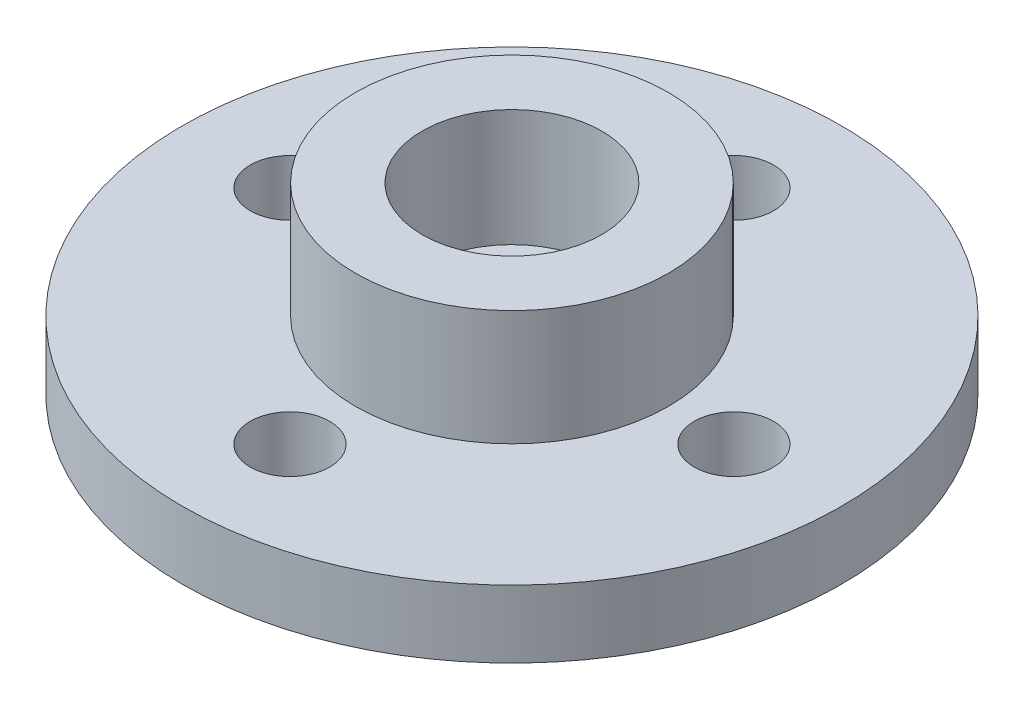
SolidWorks part; units mm, degrees
ref_plane "Front Plane" through (0, 0, 0) normal (0, 0, 1) x (1, 0, 0)
ref_plane "Top Plane" through (0, 0, 0) normal (0, 1, 0) x (1, 0, 0)
ref_plane "Right Plane" through (0, 0, 0) normal (1, 0, 0) x (0, 0, -1)
sketch "Sketch1" plane through (0, 0, 0) normal (0, 1, 0) x (1, 0, 0)
  circle A0 centre (0, 0) radius 10
  dimension "D1" = 20
extrude "Boss-Extrude1" add sketch "Sketch1" along normal blind 2.05
sketch "Sketch2" plane through (0, 2.05, 0) normal (0, 1, 0) x (1, 0, 0)
  circle A0 centre (0, 0) radius 4.75
  dimension "D1" = 9.5
extrude "Boss-Extrude2" add sketch "Sketch2" along normal blind 3.5
sketch "Sketch3" plane through (0, 5.55, 0) normal (0, 1, 0) x (1, 0, 0)
  circle A0 centre (0, 0) radius 2.725
  dimension "D1" = 5.45
extrude "Cut-Extrude1" cut sketch "Sketch3" against normal blind 3.55
sketch "Sketch4" plane through (0, 2, 0) normal (0, 1, 0) x (1, 0, 0)
  circle A0 centre (0, 0) radius 1.375
  dimension "D1" = 2.75
extrude "Cut-Extrude2" cut sketch "Sketch4" against normal blind 3.55
sketch "Sketch5" plane through (0, 0, 0) normal (0, -1, 0) x (1, 0, 0)
  circle A0 centre (-6.735, 0) radius 1.205
  dimension "D2" = 2.41
  dimension "D1" = 6.735
extrude "Cut-Extrude3" cut sketch "Sketch5" against normal blind 3.55
pattern_circular "CirPattern1" count 4 over 360 about axis through (0, 0, 0) along (0, 1, 0) of "Cut-Extrude3"
